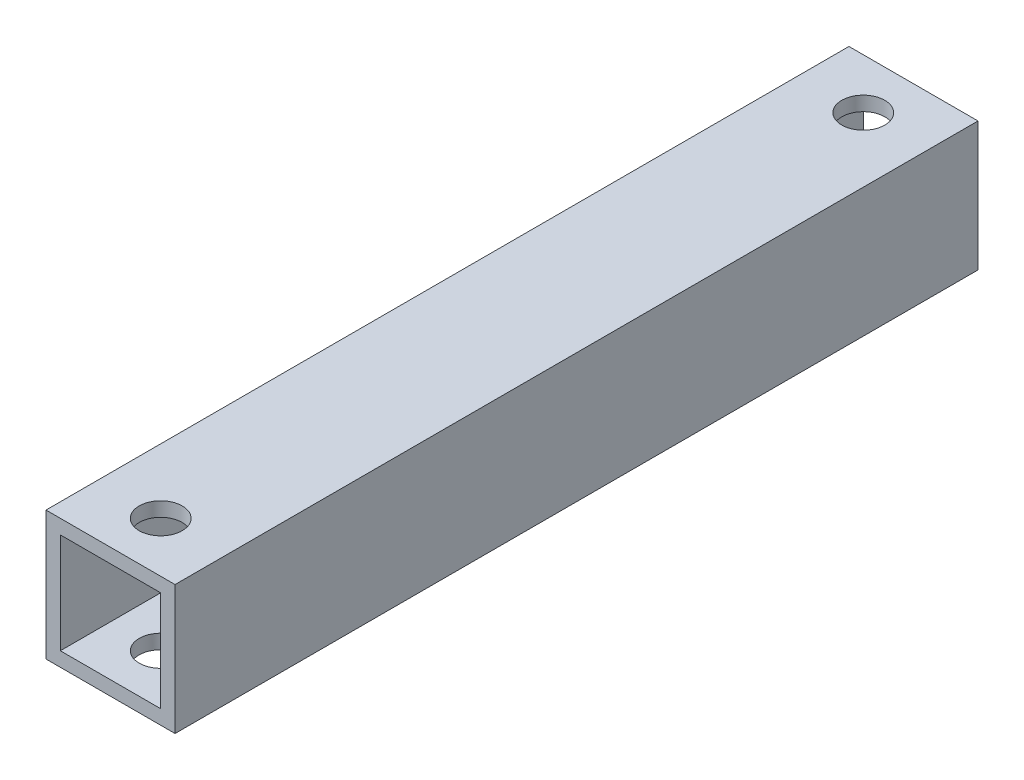
SolidWorks part; units mm, degrees
ref_plane "正面" through (0, 0, 0) normal (0, 0, 1) x (1, 0, 0)
ref_plane "平面" through (0, 0, 0) normal (0, 1, 0) x (1, 0, 0)
ref_plane "右側面" through (0, 0, 0) normal (1, 0, 0) x (0, 0, -1)
sketch "ｽｹｯﾁ1" plane through (0, 0, 0) normal (0, 0, 1) x (1, 0, 0)
  line L1 (-4.5, 4.5) -> (4.5, 4.5)
  line L2 (-4.5, 4.5) -> (-4.5, -4.5)
  line L3 (-4.5, -4.5) -> (4.5, -4.5)
  line L4 (4.5, 4.5) -> (4.5, -4.5)
  line L5 (-4.5, 4.5) -> (4.5, -4.5) construction
  line L6 (-4.5, -4.5) -> (4.5, 4.5) construction
  point P0 (0, 0)
  dimension "D1" = 9
  dimension "D2" = 9
extrude "ﾎﾞｽ - 押し出し1" add sketch "ｽｹｯﾁ1" along normal blind 56
sketch "ｽｹｯﾁ2" plane through (0, 0, 56) normal (0, 0, 1) x (1, 0, 0)
  line L1 (-3.5, 3.5) -> (3.5, 3.5)
  line L2 (-3.5, 3.5) -> (-3.5, -3.5)
  line L3 (-3.5, -3.5) -> (3.5, -3.5)
  line L4 (3.5, 3.5) -> (3.5, -3.5)
  line L5 (-3.5, 3.5) -> (3.5, -3.5) construction
  line L6 (-3.5, -3.5) -> (3.5, 3.5) construction
  point P0 (0, 0)
  dimension "D1" = 7
  dimension "D2" = 7
extrude "ｶｯﾄ - 押し出し1" cut sketch "ｽｹｯﾁ2" against normal blind 56
sketch "ｽｹｯﾁ3" plane through (0, 4.5, 0) normal (0, 1, 0) x (1, 0, 0)
  line L0 (0, 0) -> (0, -3.5)
  line L1 (0, -56) -> (0, -52.5)
  line L2 (4.5, -56) -> (-4.5, -56) construction
  circle A0 centre (0, -3.5) radius 1.5
  circle A1 centre (0, -52.5) radius 1.5
  dimension "D1" = 3
  dimension "D2" = 3
  dimension "D3" = 3.5
  dimension "D4" = 3.5
extrude "ｶｯﾄ - 押し出し2" cut sketch "ｽｹｯﾁ3" against normal blind 56
